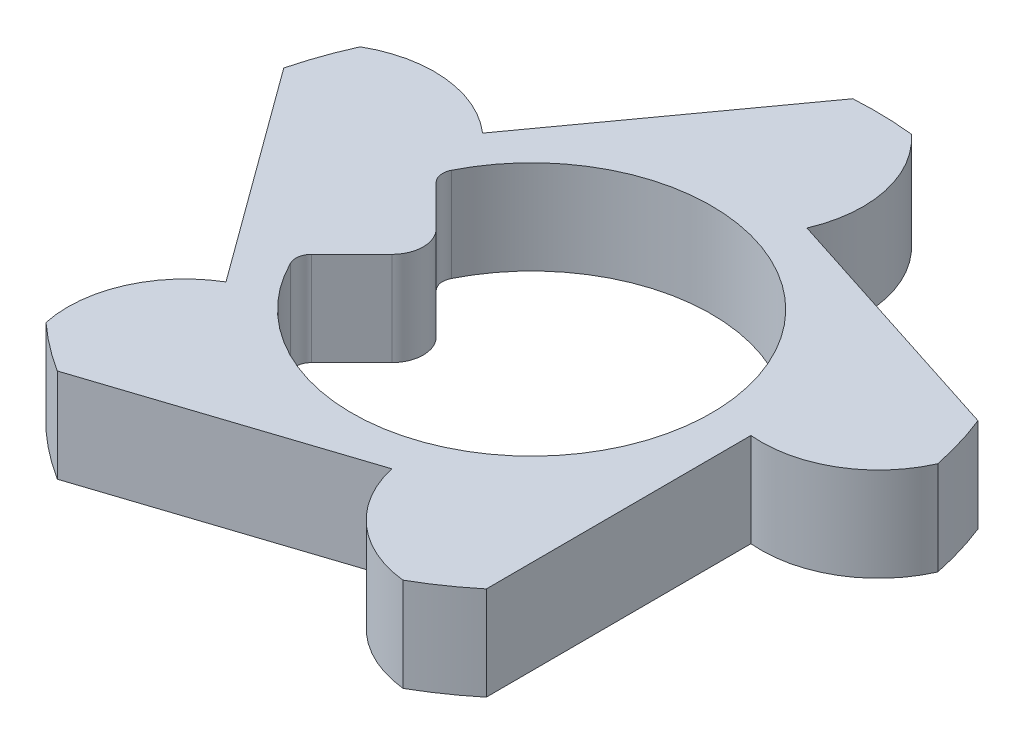
SolidWorks part; units mm, degrees
ref_plane "Front Plane" through (0, 0, 0) normal (0, 0, 1) x (1, 0, 0)
ref_plane "Top Plane" through (0, 0, 0) normal (0, 1, 0) x (1, 0, 0)
ref_plane "Right Plane" through (0, 0, 0) normal (1, 0, 0) x (0, 0, -1)
sketch "Sketch1" plane through (0, 0, 0) normal (0, 1, 0) x (1, 0, 0)
  line L0 (0, 0) -> (-1.65, 0) construction
  line L1 (0, 0) -> (-1.6298, 0.2571) construction
  line L2 (0, 0) -> (-1.3349, -0.9698) construction
  line L3 (0, 0) -> (1.65, 0) construction
  line L4 (0, 0) -> (0.4326, -1.3315) construction
  line L5 (-1.1307, -0.8255) -> (-2.1314, 0.5451)
  line L6 (0, 0) -> (0, -1.4) construction
  line L7 (0, 0) -> (-1.3349, 0.9698) construction
  line L8 (0, 0) -> (0.5099, 1.5692) construction
  line L9 (0, 0) -> (1.65, 0) construction
  line L10 (0, 0) -> (0.5099, -1.5692) construction
  line L11 (-1.1345, 0.8203) -> (-0.1402, 2.1955)
  line L12 (0.4295, 1.3325) -> (2.0447, 0.8118)
  line L13 (1.4, 0.0032) -> (1.4039, -1.6938)
  line L14 (0.4357, -1.3305) -> (-1.1771, -1.8586)
  arc A0 (-2.0044, 0.9069) -> (-2.1314, 0.5451) centre (0, 0) ccw
  circle A1 centre (0, 0) radius 1.65 construction
  circle A2 centre (0, 0) radius 1.4 construction
  arc A3 (0.2431, 2.1865) -> (-0.1402, 2.1955) centre (0, 0) ccw
  arc A4 (-1.1345, 0.8203) -> (-2.0044, 0.9069) centre (-1.6298, 0.2571) ccw
  arc A5 (0.4295, 1.3325) -> (0.2431, 2.1865) centre (-0.2591, 1.6295) ccw
  arc A6 (2.1546, 0.4445) -> (2.0447, 0.8118) centre (0, 0) ccw
  arc A7 (1.4, 0.0032) -> (2.1546, 0.4445) centre (1.4697, 0.75) ccw
  arc A8 (1.0885, -1.9118) -> (1.4039, -1.6938) centre (0, 0) ccw
  arc A9 (0.4357, -1.3305) -> (1.0885, -1.9118) centre (1.1675, -1.166) ccw
  arc A10 (-1.4819, -1.626) -> (-1.1771, -1.8586) centre (0, 0) ccw
  arc A11 (-1.1307, -0.8255) -> (-1.4819, -1.626) centre (-0.7482, -1.4706) ccw
  point P20 (0, 0)
  point P36 (0, 0)
  point P38 (0, 0)
  point P46 (0, 0)
  dimension "D1" = 4.4
  dimension "D2" = 3.3
  dimension "D3" = 2.8
  dimension "D5" = 0.75
  dimension "D4" = 72
  dimension "D6" = 72
  dimension "D7" = 5
extrude "Boss-Extrude1" add sketch "Sketch1" along normal blind 0.6
sketch "Sketch2" plane through (0, 0.6, 0) normal (0, 1, 0) x (1, 0, 0)
  line L0 (0, 0) -> (-1.15, 0) construction
  line L1 (-1.0591, 0.4481) -> (-0.611, 0)
  line L2 (-0.611, 0) -> (-1.0591, -0.4481)
  arc A0 (-1.0591, -0.4481) -> (-1.0591, 0.4481) centre (0, 0) ccw
  dimension "D1" = 2.3
  dimension "D2" = 0.611
extrude "Cut-Extrude1" cut sketch "Sketch2" against normal up to next
fillet "Fillet1" radius 0.1 2 edges at (-1.0591, 0.3, 0.4481) (-1.0591, 0.3, -0.4481)
fillet "Fillet2" radius 0.2 1 edges at (-0.611, 0.3, 0)
